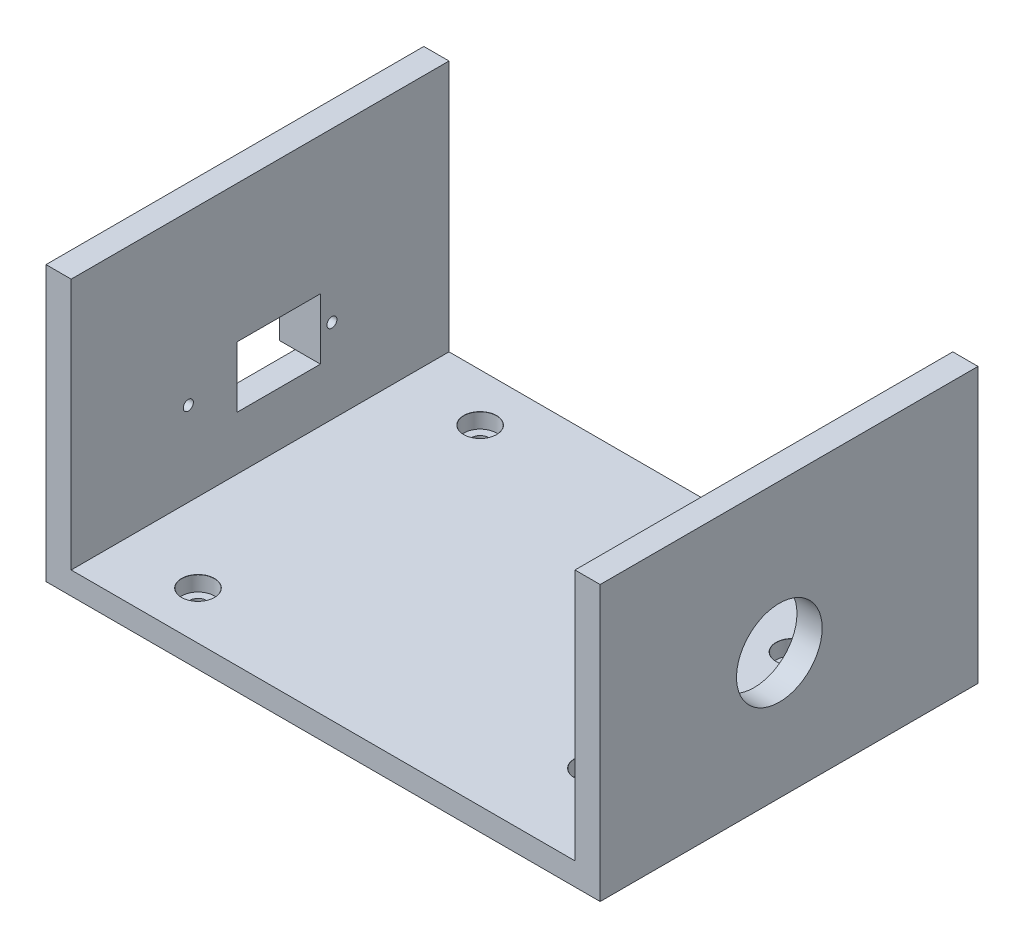
SolidWorks part; units mm, degrees
ref_plane "Front Plane" through (0, 0, 0) normal (0, 0, 1) x (1, 0, 0)
ref_plane "Top Plane" through (0, 0, 0) normal (0, 1, 0) x (1, 0, 0)
ref_plane "Right Plane" through (0, 0, 0) normal (1, 0, 0) x (0, 0, -1)
sketch "Sketch1" plane through (0, 0, 0) normal (0, 1, 0) x (1, 0, 0)
  line L1 (-38.8907, 52.202) -> (61.1093, 52.202)
  line L2 (-38.8907, 52.202) -> (-38.8907, -22.798)
  line L3 (-38.8907, -22.798) -> (61.1093, -22.798)
  line L4 (61.1093, 52.202) -> (61.1093, -22.798)
  dimension "D1" = 100
  dimension "D2" = 75
extrude "Boss-Extrude1" add sketch "Sketch1" along normal blind 4.5
sketch "Sketch2" plane through (0, 4.5, 0) normal (0, 1, 0) x (1, 0, 0)
  line L0 (-38.8907, 14.702) -> (61.1093, 14.702) construction
  line L1 (-38.8907, 52.202) -> (-38.8907, -22.798) construction
  line L2 (61.1093, -22.798) -> (61.1093, 52.202) construction
  point P9 (-23.219, 14.702)
  point P12 (46.781, 14.702)
  point P13 (-23.219, -13.298)
  point P14 (46.781, -5.298)
  point P15 (-23.219, 42.702)
  point P16 (46.781, 34.702)
hole_wizard "CBORE for M3 Socket Head Cap Screw1" positions "Sketch3" profile "Sketch4" counterbore size "M3" standard "IS" end condition through all
sketch "Sketch3" plane through (0, 4.5, 0) normal (0, 1, 0) x (1, 0, 0)
  point P0 (-23.219, 42.702)
  point P3 (-23.219, -13.298)
  point P6 (46.781, -5.298)
  point P9 (46.781, 34.702)
sketch "Sketch4" plane through (-23.219, 4.5, -42.702) normal (1, 0, 0) x (0, 0, 1)
  line L0 (0, 0) -> (0, 4.5)
  line L1 (0, 4.5) -> (1.7, 4.5)
  line L3 (1.7, 4.5) -> (1.7, 3)
  line L4 (3.25, 3) -> (1.7, 3)
  line L5 (3.25, 3) -> (3.25, 0.025)
  line L6 (3.25, 0.025) -> (3.275, 0)
  line L7 (3.275, 0) -> (0, 0)
  line L8 (-3.25, 0.025) -> (-3.275, 0) construction
  line L11 (0, -6.35) -> (0, 107.95) construction
  dimension "Thru Hole Dia." = 3.4
  dimension "Thru Hole Depth" = 4.5
  dimension "C'Bore Dia." = 6.5
  dimension "C'Bore Depth" = 3
  dimension "Near C'Sink Dia." = 6.55
  dimension "Near C'Sink Angle" = 90
sketch "Sketch5" plane through (0, 4.5, 0) normal (0, 1, 0) x (1, 0, 0)
  line L0 (-38.8907, 52.202) -> (-38.8907, -22.798)
  line L1 (-38.8907, 52.202) -> (-43.8907, 52.202)
  line L2 (-38.8907, -22.798) -> (-43.8907, -22.798)
  line L3 (-43.8907, 52.202) -> (-43.8907, -22.798)
  line L4 (61.1093, 52.202) -> (61.1093, -22.798)
  line L5 (61.1093, 52.202) -> (66.1093, 52.202)
  line L6 (61.1093, -22.798) -> (66.1093, -22.798)
  line L7 (66.1093, 52.202) -> (66.1093, -22.798)
  dimension "D1" = 5
  dimension "D2" = 5
extrude "Boss-Extrude2" add sketch "Sketch5" along normal blind 50 and the other way blind 4.5
sketch "Sketch6" plane through (-43.8907, 0, 0) normal (-1, 0, 0) x (0, 0, 1)
  line L0 (-30.952, 15.15) -> (-30.952, 27.25) construction
  line L1 (-30.952, 27.25) -> (1.548, 27.25) construction
  line L2 (1.548, 27.25) -> (1.548, 15.15) construction
  line L3 (1.548, 15.15) -> (-30.952, 15.15) construction
  line L4 (-14.702, 54.5) -> (-14.702, 27.25) construction
  line L5 (-52.202, 54.5) -> (22.798, 54.5) construction
  line L6 (-52.202, 0) -> (22.798, 0) construction
  line L7 (-10.0716, 21.2) -> (1.548, 21.2) construction
  line L10 (-14.702, 15.15) -> (-14.702, 0) construction
  line L11 (-26.6706, 27.25) -> (-26.6706, 15.15)
  line L12 (-26.6706, 15.15) -> (-10.0716, 15.15)
  line L13 (-10.0716, 15.15) -> (-10.0716, 27.25)
  line L14 (-10.0716, 27.25) -> (-26.6706, 27.25)
  circle A0 centre (-28.952, 21.2) radius 1
  circle A1 centre (-0.452, 21.2) radius 1
  dimension "D4" = 2
  dimension "D1" = 2
  dimension "D2" = 32.5
  dimension "D3" = 12.1
  dimension "D5" = 2
sketch "Sketch7" plane through (-43.8907, 0, 0) normal (-1, 0, 0) x (0, 0, 1)
  line L0 (-26.452, 27.25) -> (-26.452, 15.15)
  line L1 (-30.952, 15.15) -> (1.548, 15.15)
  line L2 (-30.952, 15.15) -> (-30.952, 27.25)
  line L3 (-30.952, 27.25) -> (1.548, 27.25)
  line L4 (1.548, 15.15) -> (1.548, 27.25)
  line L5 (-2.952, 27.25) -> (-2.952, 15.15)
  dimension "D1" = 23.5
  dimension "D2" = 4.5
extrude "Boss-Extrude3" add sketch "Sketch7" along normal blind 3.1 contours L3 L2 L1 L0 | L3 L5 L1 L4
extrude "Cut-Extrude1" cut sketch "Sketch6" against normal blind 9.1 and the other way blind 10 contours A0 | L14 L11 L12 L13 | A1
sketch "Sketch8" plane through (66.1093, 0, 0) normal (1, 0, 0) x (0, 0, -1)
  line L0 (-22.798, 0) -> (52.202, 0) construction
  circle A0 centre (12.7677, 25) radius 8.5
  point P2 (0, 0)
  dimension "D1" = 17
  dimension "D2" = 25
extrude "Cut-Extrude2" cut sketch "Sketch8" against normal blind 9.1
